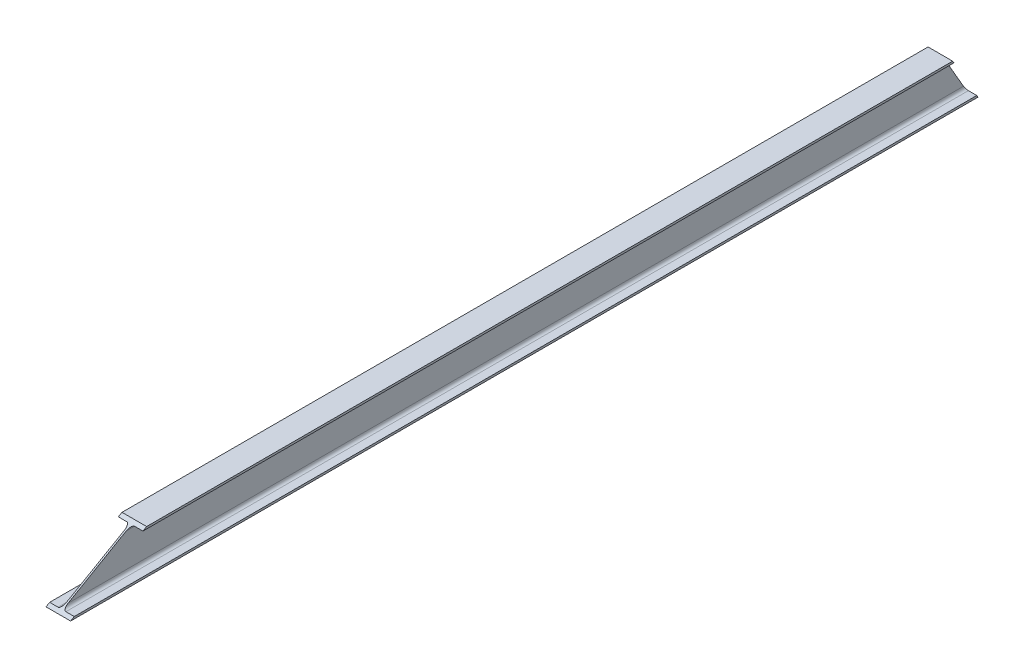
SolidWorks part; units mm, degrees
material "1.0035 (S185)"
ref_plane "Front Plane" through (0, 0, 0) normal (0, 0, 1) x (1, 0, 0)
ref_plane "Top Plane" through (0, 0, 0) normal (0, 1, 0) x (1, 0, 0)
ref_plane "Right Plane" through (0, 0, 0) normal (1, 0, 0) x (0, 0, -1)
sketch "Sketch1" plane through (0, 0, 0) normal (0, 0, 1) x (1, 0, 0)
  line L0 (-27.5, 49) -> (27.5, 49)
  line L1 (27.5, 49) -> (27.5, 44.3)
  line L2 (27.5, 44.3) -> (8.8, 44.3)
  line L3 (1.8, 37.3) -> (1.8, -37.3)
  line L4 (8.8, -44.3) -> (27.5, -44.3)
  line L5 (27.5, -44.3) -> (27.5, -49)
  line L6 (27.5, -49) -> (-27.5, -49)
  line L7 (-27.5, -49) -> (-27.5, -44.3)
  line L8 (-27.5, -44.3) -> (-8.8, -44.3)
  line L9 (-1.8, -37.3) -> (-1.8, 37.3)
  line L10 (-8.8, 44.3) -> (-27.5, 44.3)
  line L11 (-27.5, 44.3) -> (-27.5, 49)
  line L12 (-36.0742, 0) -> (31.9951, 0) construction
  arc A0 (8.8, -44.3) -> (1.8, -37.3) centre (8.8, -37.3) cw
  arc A1 (-1.8, -37.3) -> (-8.8, -44.3) centre (-8.8, -37.3) cw
  arc A2 (-8.8, 44.3) -> (-1.8, 37.3) centre (-8.8, 37.3) cw
  arc A3 (1.8, 37.3) -> (8.8, 44.3) centre (8.8, 37.3) cw
  dimension "D8" = 7
  dimension "D2" = 3.6
  dimension "D3" = 4.7
  dimension "D4" = 4.7
  dimension "D5" = 1.8
  dimension "D6" = 55
  dimension "D7" = 25.7
  dimension "D1" = 98
  dimension "D9" = 49
extrude "Boss-Extrude1" add sketch "Sketch1" along normal blind 2032
ref_plane "Plane1" through (0, -12.25, 21.2176) normal (0, -0.5, 0.866) x (1, 0, 0)
sketch "Sketch2" plane through (0, -12.25, 21.2176) normal (0, -0.5, 0.866) x (1, 0, 0)
  line L1 (-105.8512, -228.7626) -> (105.8512, -228.7626)
  line L2 (-105.8512, -228.7626) -> (-105.8512, 254.8243)
  line L3 (-105.8512, 254.8243) -> (105.8512, 254.8243)
  line L4 (105.8512, -228.7626) -> (105.8512, 254.8243)
  line L5 (-105.8512, -228.7626) -> (105.8512, 254.8243) construction
  line L6 (-105.8512, 254.8243) -> (105.8512, -228.7626) construction
  point P0 (0, 13.0309)
extrude "Cut-Extrude1" cut sketch "Sketch2" against normal through all
ref_plane "Plane2" through (0, 0, 2032) normal (0, 0, 1) x (1, 0, 0)
ref_plane "Plane3" through (0, 843.1318, 486.7824) normal (0, 0.866, 0.5) x (1, 0, 0)
sketch "Sketch3" plane through (0, 843.1318, 486.7824) normal (0, 0.866, 0.5) x (1, 0, 0)
  line L1 (-93.3263, -1941.581) -> (107.2856, -1941.581)
  line L2 (-93.3263, -1941.581) -> (-93.3263, -1084.1593)
  line L3 (-93.3263, -1084.1593) -> (107.2856, -1084.1593)
  line L4 (107.2856, -1941.581) -> (107.2856, -1084.1593)
  line L5 (-93.3263, -1941.581) -> (107.2856, -1084.1593) construction
  line L6 (-93.3263, -1084.1593) -> (107.2856, -1941.581) construction
  point P0 (6.9797, -1512.8702)
extrude "Cut-Extrude3" cut sketch "Sketch3" against normal blind 2.54 and the other way through all
equation "\"D4@Sketch1\"=\"D3@Sketch1\""
equation "\"D5@Sketch1\"=\"D2@Sketch1\"/2"
equation "\"D7@Sketch1\"=(\"D6@Sketch1\"-\"D2@Sketch1\")/2"
equation "\"D9@Sketch1\"=\"D1@Sketch1\"/2"
